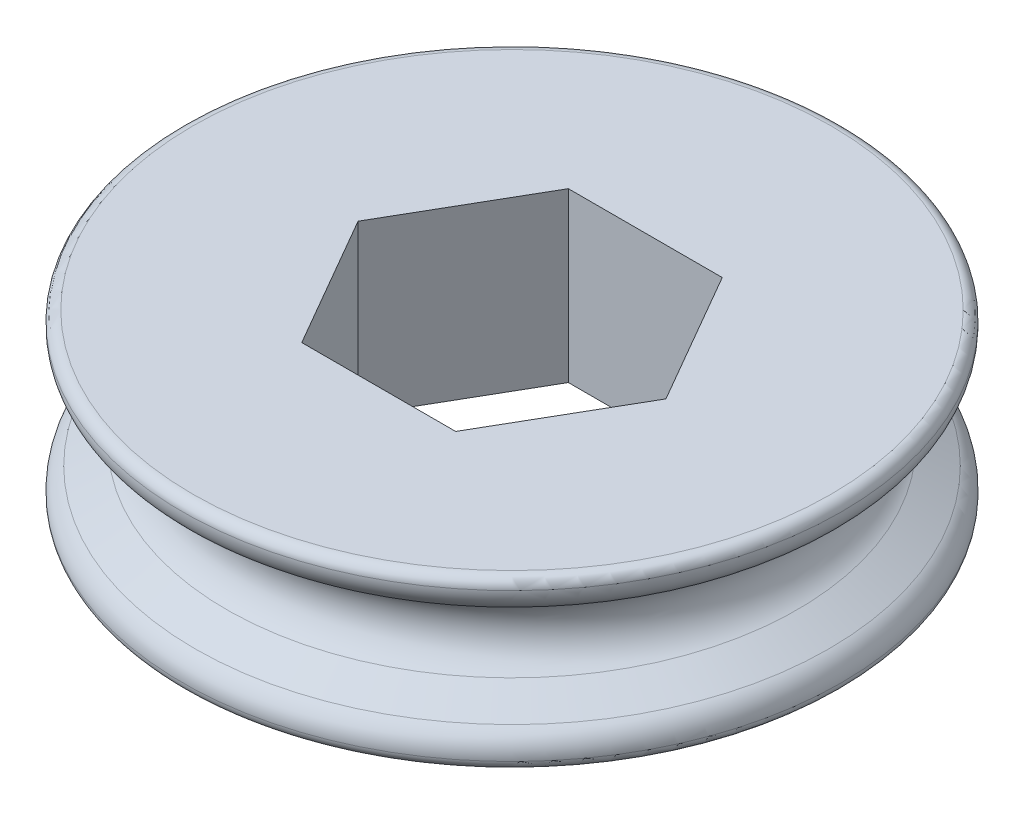
SolidWorks part; units mm, degrees
ref_plane "Front Plane" through (0, 0, 0) normal (0, 0, 1) x (1, 0, 0)
ref_plane "Top Plane" through (0, 0, 0) normal (0, 1, 0) x (1, 0, 0)
ref_plane "Right Plane" through (0, 0, 0) normal (1, 0, 0) x (0, 0, -1)
sketch "Sketch1" plane through (0, 0, 0) normal (0, 0, 1) x (0, 1, 0)
  line L0 (0, 0) -> (0, 17451.5356) construction
  line L1 (4, 0) -> (-4, 0)
  line L2 (-4, 0) -> (-4, 15.2006)
  line L3 (4, 0) -> (4, 15.2006)
  line L6 (-2.4257, 15.1015) -> (-1.5588, 13.6)
  line L7 (2.4257, 15.1015) -> (1.5588, 13.6)
  arc A0 (-4, 15.2006) -> (-3.525, 15.7) centre (-3.5, 15.2006) cw
  arc A1 (4, 15.2006) -> (3.525, 15.7) centre (3.5, 15.2006) ccw
  arc A2 (-3.525, 15.7) -> (-2.4257, 15.1015) centre (-3.465, 14.5015) cw
  arc A3 (3.525, 15.7) -> (2.4257, 15.1015) centre (3.465, 14.5015) ccw
  arc A4 (-1.5588, 13.6) -> (1.5588, 13.6) centre (0, 14.5) ccw
  point P6 (0, 0)
  point P18 (0, 12.7)
  dimension "D2" = 0.5
  dimension "D4" = 1.2
  dimension "D5" = 1.8
  dimension "D1" = 8
  dimension "D3" = 12.7
  dimension "D6" = 3
  dimension "D7" = 60
revolve "Revolve1" add sketch "Sketch1" angle 360 about L1
sketch "Sketch2" plane through (0, -4, 0) normal (0, -1, 0) x (1, 0, 0)
  line L1 (7.3323, 0) -> (3.6662, 6.35)
  line L2 (3.6662, 6.35) -> (-3.6662, 6.35)
  line L3 (-3.6662, 6.35) -> (-7.3323, 0)
  line L4 (-7.3323, 0) -> (-3.6662, -6.35)
  line L5 (-3.6662, -6.35) -> (3.6662, -6.35)
  line L6 (3.6662, -6.35) -> (7.3323, 0)
  circle A1 centre (0, 0) radius 15.2006
  circle A2 centre (0, 0) radius 15.2006
  circle A3 centre (0, 0) radius 6.35 construction
  dimension "D2" = 12.7
  dimension "D1" = 0
extrude "Cut-Extrude2" cut sketch "Sketch2" against normal through all contours L1 L2 L3 L4 L5 L6
